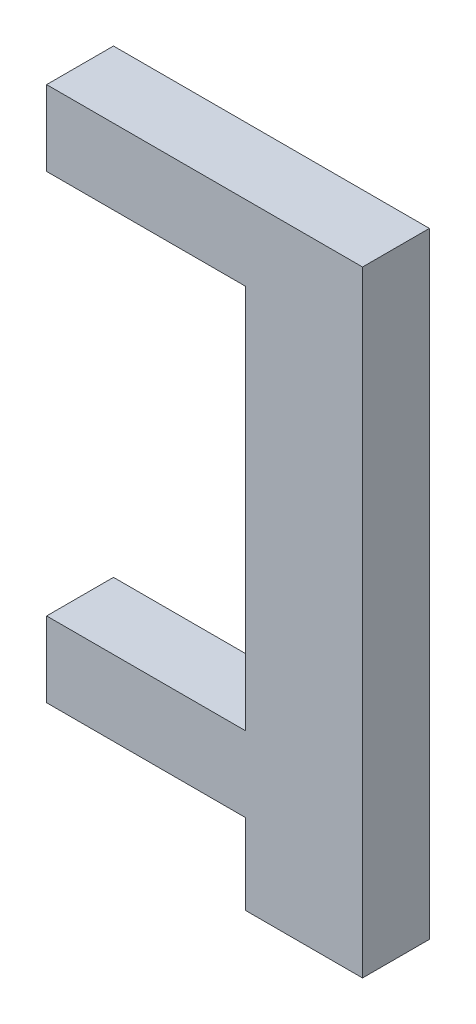
SolidWorks part; units mm, degrees
material "Balsa"
ref_plane "Front Plane" through (0, 0, 0) normal (0, 0, 1) x (1, 0, 0)
ref_plane "Top Plane" through (0, 0, 0) normal (0, 1, 0) x (1, 0, 0)
ref_plane "Right Plane" through (0, 0, 0) normal (1, 0, 0) x (0, 0, -1)
sketch "Sketch5" plane through (0, 0, 0) normal (0, 0, 1) x (1, 0, 0)
  line L0 (0, 0) -> (0, 36.84)
  line L1 (0, 36.84) -> (-18.9, 36.84)
  line L2 (-18.9, 36.84) -> (-18.9, 32.34)
  line L3 (-18.9, 32.34) -> (-7, 32.34)
  line L4 (-7, 32.34) -> (-7, 9.31)
  line L5 (-7, 9.31) -> (-18.9, 9.31)
  line L6 (-18.9, 9.31) -> (-18.9, 4.81)
  line L7 (-18.9, 4.81) -> (-7, 4.81)
  line L8 (-7, 4.81) -> (-7, 0)
  line L9 (-7, 0) -> (0, 0)
  dimension "D1" = 4.5
  dimension "D2" = 23.03
  dimension "D3" = 11.9
  dimension "D4" = 4.81
  dimension "D5" = 7
extrude "Boss-Extrude1" add sketch "Sketch5" along normal blind 4
